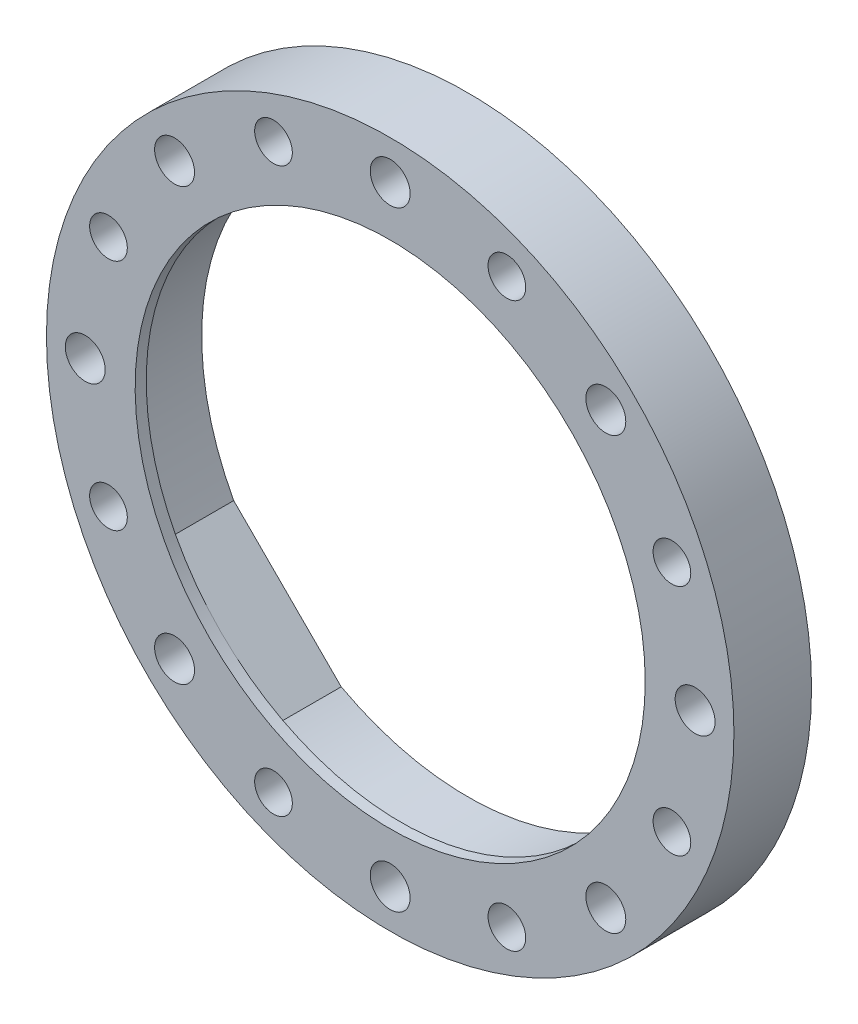
SolidWorks part; units mm, degrees
material "ABS"
ref_plane "正面" through (0, 0, 0) normal (0, 0, 1) x (1, 0, 0)
ref_plane "平面" through (0, 0, 0) normal (0, 1, 0) x (1, 0, 0)
ref_plane "右側面" through (0, 0, 0) normal (1, 0, 0) x (0, 0, -1)
sketch "ｽｹｯﾁ1" plane through (0, 0, 0) normal (0, 0, 1) x (1, 0, 0)
  circle A0 centre (0, 0) radius 31
  dimension "D1" = 62
extrude "ﾎﾞｽ - 押し出し1" add sketch "ｽｹｯﾁ1" along normal blind 6
sketch "ｽｹｯﾁ2" plane through (0, 0, 6) normal (0, 0, 1) x (1, 0, 0)
  circle A0 centre (0, 0) radius 24
  dimension "D1" = 48
extrude "ｶｯﾄ - 押し出し1" cut sketch "ｽｹｯﾁ2" against normal through all
sketch "ｽｹｯﾁ3" plane through (0, 0, 6) normal (0, 0, 1) x (1, 0, 0)
  line L1 (-32.5269, 0) -> (0, 32.5269)
  line L2 (-32.5269, 0) -> (0, -32.5269)
  line L3 (0, -32.5269) -> (32.5269, 0)
  line L4 (0, 32.5269) -> (32.5269, 0)
  line L5 (-32.5269, 0) -> (32.5269, 0) construction
  line L6 (0, -32.5269) -> (0, 32.5269) construction
  circle A1 centre (0, 0) radius 24
  circle A2 centre (0, 0) radius 24 construction
  point P0 (0, 0)
  circle M5 centre (0, 0) radius 24
  dimension "D1" = 46
extrude "ﾎﾞｽ - 押し出し2" add sketch "ｽｹｯﾁ3" against normal through all contours L2 M5 | L3 M5 | L4 M5 | L1 M5 | A1
sketch "ｽｹｯﾁ5" plane through (0, 0, 6) normal (0, 0, 1) x (1, 0, 0)
  line L0 (11.4158, -21.1111) -> (21.1111, -11.4158) construction
  circle A0 centre (0, 0) radius 31
  circle A1 centre (0, 0) radius 23
  circle A2 centre (0, 0) radius 31 construction
extrude "ﾎﾞｽ - 押し出し3" add sketch "ｽｹｯﾁ5" along normal blind 1
hole_wizard "M3 すきま穴1" positions "ｽｹｯﾁ6" profile "ｽｹｯﾁ7" hole size "M3" standard "JIS" end condition through all
sketch "ｽｹｯﾁ6" plane through (0, 0, 7) normal (0, 0, 1) x (1, 0, 0)
  circle A1 centre (0, 0) radius 27.5 construction
  circle A2 centre (0, 0) radius 31 construction
  point P0 (0, 27.5)
  dimension "D1" = 3.5
sketch "ｽｹｯﾁ7" plane through (0, 27.5, 7) normal (1, 0, 0) x (0, -1, 0)
  line L0 (0, 0) -> (0, 7)
  line L1 (0, 7) -> (1.8, 7)
  line L2 (1.8, 7) -> (1.8, 0)
  line L5 (1.8, 0) -> (0, 0)
  line L11 (0, -6.35) -> (0, 107.95) construction
  dimension "通し穴の直径" = 3.6
  dimension "通し穴の深さ" = 7
pattern_circular "円形ﾊﾟﾀｰﾝ1" count 8 over 360 about axis through (0, 0, 0) along (0, 0, 1) of "M3 すきま穴1"
sketch "ｽｹｯﾁ8" plane through (0, 0, 0) normal (0, 0, -1) x (-1, 0, 0)
  line L1 (-41.0122, 0) -> (0, -41.0122)
  line L2 (-41.0122, 0) -> (0, 41.0122)
  line L3 (0, 41.0122) -> (41.0122, 0)
  line L4 (0, -41.0122) -> (41.0122, 0)
  line L5 (-41.0122, 0) -> (41.0122, 0) construction
  line L6 (0, 41.0122) -> (0, -41.0122) construction
  circle A0 centre (0, 0) radius 31 construction
  point P0 (0, 0)
  circle M19 centre (0, 0) radius 31
  circle M21 centre (-19.4454, -19.4454) radius 1.8
  circle M23 centre (19.4454, 19.4454) radius 1.8
  dimension "D1" = 29
extrude "ｶｯﾄ - 押し出し2" [suppressed] cut sketch "ｽｹｯﾁ8" against normal through all contours L1 M19 M21 | L3 M19 M23
hole_wizard "M3 すきま穴2" positions "ｽｹｯﾁ9" profile "ｽｹｯﾁ10" hole size "M3" standard "JIS" end condition through all
sketch "ｽｹｯﾁ9" plane through (0, 0, 7) normal (0, 0, 1) x (1, 0, 0)
  arc A1 (0, 27.5) -> (19.4454, 19.4454) centre (0, 0) cw construction
  point P0 (10.5238, 25.4067)
sketch "ｽｹｯﾁ10" plane through (10.5238, 25.4067, 7) normal (1, 0, 0) x (0, -1, 0)
  line L0 (0, 0) -> (0, 7)
  line L1 (0, 7) -> (1.7, 7)
  line L2 (1.7, 7) -> (1.7, 0)
  line L5 (1.7, 0) -> (0, 0)
  line L11 (0, -6.35) -> (0, 107.95) construction
  dimension "通し穴の直径" = 3.4
  dimension "通し穴の深さ" = 7
sketch "ｽｹｯﾁ11" plane through (0, 0, 0) normal (0, 0, -1) x (-1, 0, 0)
  line L0 (-10.5238, 25.4067) -> (0, 0) construction
  line L1 (-7.9588, 23.4385) -> (-7.5367, 26.644)
  line L2 (-7.5367, 26.644) -> (-10.1018, 28.6122)
  line L3 (-10.1018, 28.6122) -> (-13.0888, 27.3749)
  line L4 (-13.0888, 27.3749) -> (-13.5108, 24.1694)
  line L5 (-13.5108, 24.1694) -> (-10.9458, 22.2012)
  line L6 (-10.9458, 22.2012) -> (-7.9588, 23.4385)
  circle A1 centre (-10.5238, 25.4067) radius 2.8 construction
  dimension "D1" = 5.6
extrude "ｶｯﾄ - 押し出し3" [suppressed] cut sketch "ｽｹｯﾁ11" against normal blind 2.6
sketch "ｽｹｯﾁ12" [suppressed] plane through (0, 0, 0) normal (0, 0, -1) x (-1, 0, 0)
  circle A0 centre (-10.1018, 28.6122) radius 0.5
  dimension "D1" = 1
extrude "ｶｯﾄ - 押し出し4" [suppressed] cut sketch "ｽｹｯﾁ12" against normal up to surface (2.6 mm away)
pattern_circular "円形ﾊﾟﾀｰﾝ3" [suppressed] count 6 over 360
pattern_circular "円形ﾊﾟﾀｰﾝ4" count 8 over 360 about axis through (0, 0, 0) along (0, 0, 1) of "円形ﾊﾟﾀｰﾝ3", "ｶｯﾄ - 押し出し4", "M3 すきま穴2", "ｶｯﾄ - 押し出し3"
